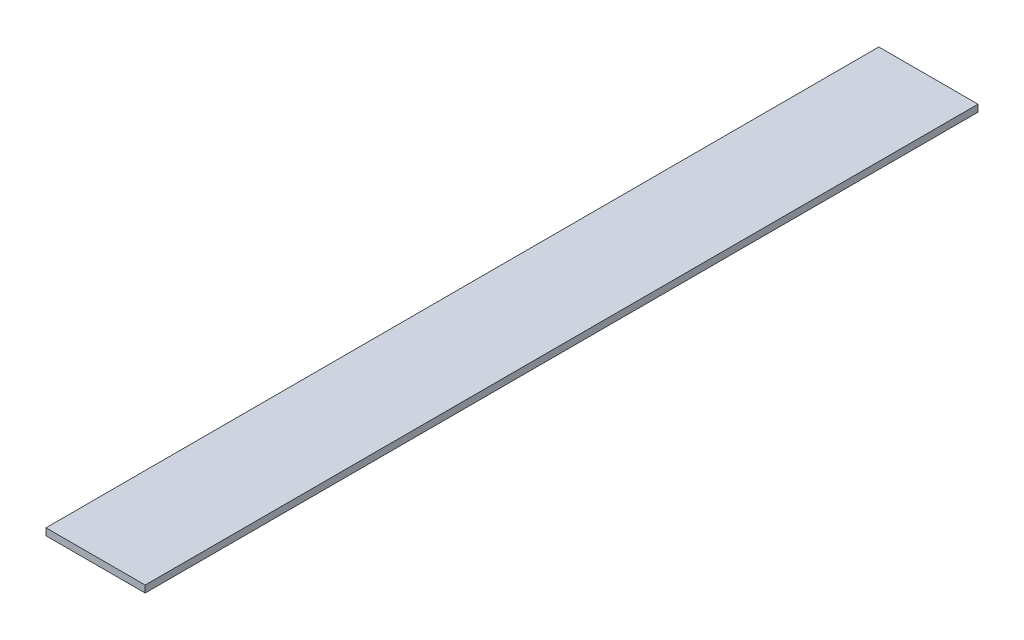
SolidWorks part; units mm, degrees
ref_plane "Front Plane" through (0, 0, 0) normal (0, 0, 1) x (1, 0, 0)
ref_plane "Top Plane" through (0, 0, 0) normal (0, 1, 0) x (1, 0, 0)
ref_plane "Right Plane" through (0, 0, 0) normal (1, 0, 0) x (0, 0, -1)
sketch "Sketch1" plane through (0, 0, 0) normal (0, 0, 1) x (1, 0, 0)
  line L0 (0, 40.0082) -> (0, -35.5491) construction
  line L1 (-58.464, 0) -> (79.7687, 0) construction
  line L2 (-31.0997, 7) -> (68.9003, 7)
  line L3 (-31.0997, 7) -> (-31.0997, 0)
  line L4 (-31.0997, 0) -> (68.9003, 0)
  line L5 (68.9003, 0) -> (68.9003, 7)
extrude "Boss-Extrude1" add sketch "Sketch1" along normal blind 840
